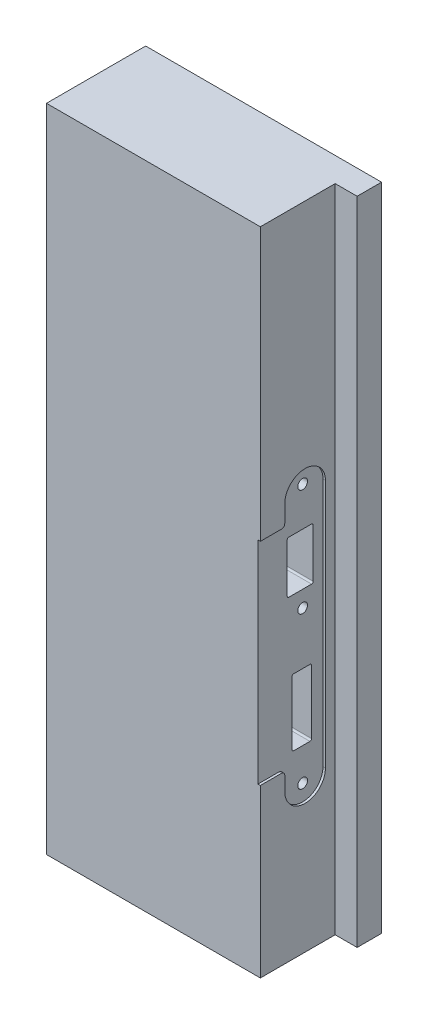
SolidWorks part; units mm, degrees
ref_plane "Plan de face" through (0, 0, 0) normal (0, 0, 1) x (1, 0, 0)
ref_plane "Plan de dessus" through (0, 0, 0) normal (0, 1, 0) x (1, 0, 0)
ref_plane "Plan de droite" through (0, 0, 0) normal (1, 0, 0) x (0, 0, -1)
sketch "Esquisse2" plane through (405.3935, 0, 0) normal (-1, 0, 0) x (0, 0, 1)
  line L0 (-30.5517, -238.2531) -> (-30.5517, -405.7531)
  line L1 (-30.5517, -535.7531) -> (-30.5517, -638.2531)
  line L2 (-30.5517, -407.7531) -> (-30.5517, -533.7531) construction
  line L4 (-76.5517, -238.2531) -> (-76.5517, -638.2531)
  line L5 (-76.5517, -638.2531) -> (-36.5517, -638.2531)
  line L6 (-70.5517, -393.2531) -> (-70.5517, -546.5031)
  line L7 (-45.5517, -546.5031) -> (-45.5517, -537.7531)
  line L8 (-43.5517, -535.7531) -> (-32.5517, -535.7531)
  line L9 (-30.5517, -533.7531) -> (-30.5517, -407.7531)
  line L10 (-32.5517, -405.7531) -> (-43.5517, -405.7531)
  line L11 (-45.5517, -403.7531) -> (-45.5517, -393.2531)
  line L12 (-70.5517, -393.2531) -> (-70.5517, -546.5031)
  line L13 (-45.5517, -546.5031) -> (-45.5517, -537.7531)
  line L14 (-43.5517, -535.7531) -> (-30.5517, -535.7531)
  line L16 (-30.5517, -405.7531) -> (-43.5517, -405.7531)
  line L17 (-45.5517, -403.7531) -> (-45.5517, -393.2531)
  line L18 (-36.5517, -638.2531) -> (-36.5517, -238.2531)
  line L19 (-36.5517, -238.2531) -> (-76.5517, -238.2531)
  line L20 (-76.5517, -238.2531) -> (-76.5517, -638.2531)
  line L21 (-76.5517, -638.2531) -> (-30.5517, -638.2531)
  line L23 (-30.5517, -238.2531) -> (-76.5517, -238.2531)
  arc A6 (-45.5517, -393.2531) -> (-70.5517, -393.2531) centre (-58.0517, -393.2531) ccw
  arc A7 (-70.5517, -546.5031) -> (-45.5517, -546.5031) centre (-58.0517, -546.5031) ccw
  arc A8 (-43.5517, -535.7531) -> (-45.5517, -537.7531) centre (-43.5517, -537.7531) ccw
  arc A9 (-32.5517, -535.7531) -> (-30.5517, -533.7531) centre (-32.5517, -533.7531) ccw
  arc A10 (-30.5517, -407.7531) -> (-32.5517, -405.7531) centre (-32.5517, -407.7531) ccw
  arc A11 (-45.5517, -403.7531) -> (-43.5517, -405.7531) centre (-43.5517, -403.7531) ccw
  arc A12 (-45.5517, -393.2531) -> (-70.5517, -393.2531) centre (-58.0517, -393.2531) ccw
  arc A13 (-70.5517, -546.5031) -> (-45.5517, -546.5031) centre (-58.0517, -546.5031) ccw
  arc A14 (-43.5517, -535.7531) -> (-45.5517, -537.7531) centre (-43.5517, -537.7531) ccw
  arc A17 (-45.5517, -403.7531) -> (-43.5517, -405.7531) centre (-43.5517, -403.7531) ccw
  dimension "D1" = 0
  dimension "D2" = 0
extrude "Extrusion1" add sketch "Esquisse2" against normal up to surface (1.5 mm away)
sketch "Esquisse3" plane through (405.3935, 0, 0) normal (-1, 0, 0) x (0, 0, 1)
  line L0 (-30.5517, -238.2531) -> (-76.5517, -238.2531) construction
  line L1 (-30.5517, -238.2531) -> (-76.5517, -238.2531)
  line L2 (-76.5517, -238.2531) -> (-76.5517, -638.2531) construction
  line L3 (-76.5517, -238.2531) -> (-76.5517, -638.2531)
  line L4 (-30.5517, -405.7531) -> (-30.5517, -238.2531) construction
  line L5 (-30.5517, -638.2531) -> (-30.5517, -238.2531)
  line L6 (-76.5517, -638.2531) -> (-30.5517, -638.2531) construction
  line L7 (-76.5517, -638.2531) -> (-30.5517, -638.2531)
extrude "Extrusion2" add sketch "Esquisse3" along normal blind 130
sketch "Esquisse4" plane through (275.3935, 0, 0) normal (-1, 0, 0) x (0, 0, 1)
  line L1 (-76.5517, -238.2531) -> (-91.5517, -238.2531)
  line L2 (-76.5517, -238.2531) -> (-76.5517, -638.2531)
  line L3 (-76.5517, -638.2531) -> (-91.5517, -638.2531)
  line L4 (-91.5517, -238.2531) -> (-91.5517, -638.2531)
  line L5 (-76.5517, -638.2531) -> (-30.5517, -638.2531) construction
  dimension "D1" = 15
extrude "Extrusion3" add sketch "Esquisse4" against normal blind 145
ref_plane "Plan1" through (520.3935, 0, 0) normal (1, 0, 0) x (0, 0, -1)
sketch "Esquisse6" plane through (520.3935, 0, 0) normal (1, 0, 0) x (0, 0, -1)
  line L4 (63.5517, -413.7531) -> (49.5517, -413.7531)
  line L5 (64.5517, -444.7531) -> (64.5517, -414.7531)
  line L18 (49.5517, -445.7531) -> (63.5517, -445.7531)
  line L19 (48.5517, -414.7531) -> (48.5517, -444.7531)
  line L20 (63.5517, -413.7531) -> (49.5517, -413.7531)
  line L21 (64.5517, -444.7531) -> (64.5517, -414.7531)
  line L22 (49.5517, -445.7531) -> (63.5517, -445.7531)
  line L23 (48.5517, -414.7531) -> (48.5517, -444.7531)
  line L24 (51.5517, -489.0031) -> (51.5517, -528.0031)
  line L25 (62.5517, -488.0031) -> (52.5517, -488.0031)
  line L26 (63.5517, -528.0031) -> (63.5517, -489.0031)
  line L27 (52.5517, -529.0031) -> (62.5517, -529.0031)
  line L28 (51.5517, -489.0031) -> (51.5517, -528.0031)
  line L29 (62.5517, -488.0031) -> (52.5517, -488.0031)
  line L30 (63.5517, -528.0031) -> (63.5517, -489.0031)
  line L31 (52.5517, -529.0031) -> (62.5517, -529.0031)
  circle A1 centre (58.0517, -389.7531) radius 3
  circle A2 centre (58.0517, -389.7531) radius 3
  circle A3 centre (58.0517, -455.7531) radius 3
  circle A4 centre (58.0517, -455.7531) radius 3
  circle A5 centre (58.0517, -549.0031) radius 3
  circle A6 centre (58.0517, -549.0031) radius 3
  arc A20 (64.5517, -414.7531) -> (63.5517, -413.7531) centre (63.5517, -414.7531) ccw
  arc A21 (63.5517, -445.7531) -> (64.5517, -444.7531) centre (63.5517, -444.7531) ccw
  arc A22 (48.5517, -444.7531) -> (49.5517, -445.7531) centre (49.5517, -444.7531) ccw
  arc A23 (49.5517, -413.7531) -> (48.5517, -414.7531) centre (49.5517, -414.7531) ccw
  arc A24 (64.5517, -414.7531) -> (63.5517, -413.7531) centre (63.5517, -414.7531) ccw
  arc A25 (63.5517, -445.7531) -> (64.5517, -444.7531) centre (63.5517, -444.7531) ccw
  arc A26 (48.5517, -444.7531) -> (49.5517, -445.7531) centre (49.5517, -444.7531) ccw
  arc A27 (49.5517, -413.7531) -> (48.5517, -414.7531) centre (49.5517, -414.7531) ccw
  arc A30 (51.5517, -528.0031) -> (52.5517, -529.0031) centre (52.5517, -528.0031) ccw
  arc A31 (52.5517, -488.0031) -> (51.5517, -489.0031) centre (52.5517, -489.0031) ccw
  arc A32 (63.5517, -489.0031) -> (62.5517, -488.0031) centre (62.5517, -489.0031) ccw
  arc A33 (62.5517, -529.0031) -> (63.5517, -528.0031) centre (62.5517, -528.0031) ccw
  arc A34 (51.5517, -528.0031) -> (52.5517, -529.0031) centre (52.5517, -528.0031) ccw
  arc A35 (52.5517, -488.0031) -> (51.5517, -489.0031) centre (52.5517, -489.0031) ccw
  arc A36 (63.5517, -489.0031) -> (62.5517, -488.0031) centre (62.5517, -489.0031) ccw
  arc A37 (62.5517, -529.0031) -> (63.5517, -528.0031) centre (62.5517, -528.0031) ccw
  dimension "D1" = 0
  dimension "D3" = 0
  dimension "D4" = 0
  dimension "D5" = 0
  dimension "D6" = 0
sketch "Esquisse7" plane through (405.3935, 0, 0) normal (1, 0, 0) x (0, 0, -1)
  line L4 (48.5517, -414.7531) -> (48.5517, -444.7531)
  line L5 (49.5517, -445.7531) -> (63.5517, -445.7531)
  line L6 (64.5517, -444.7531) -> (64.5517, -414.7531)
  line L7 (63.5517, -413.7531) -> (49.5517, -413.7531)
  line L8 (48.5517, -414.7531) -> (48.5517, -444.7531)
  line L9 (49.5517, -445.7531) -> (63.5517, -445.7531)
  line L10 (64.5517, -444.7531) -> (64.5517, -414.7531)
  line L11 (63.5517, -413.7531) -> (49.5517, -413.7531)
  line L12 (63.5517, -528.0031) -> (63.5517, -489.0031)
  line L13 (62.5517, -488.0031) -> (52.5517, -488.0031)
  line L14 (51.5517, -489.0031) -> (51.5517, -528.0031)
  line L15 (52.5517, -529.0031) -> (62.5517, -529.0031)
  line L16 (63.5517, -528.0031) -> (63.5517, -489.0031)
  line L17 (62.5517, -488.0031) -> (52.5517, -488.0031)
  line L18 (51.5517, -489.0031) -> (51.5517, -528.0031)
  line L19 (52.5517, -529.0031) -> (62.5517, -529.0031)
  circle A1 centre (58.0517, -389.7531) radius 3
  circle A2 centre (58.0517, -389.7531) radius 3
  circle A3 centre (58.0517, -455.7531) radius 3
  circle A4 centre (58.0517, -455.7531) radius 3
  circle A5 centre (58.0517, -549.0031) radius 3
  circle A6 centre (58.0517, -549.0031) radius 3
  arc A10 (48.5517, -444.7531) -> (49.5517, -445.7531) centre (49.5517, -444.7531) ccw
  arc A11 (63.5517, -445.7531) -> (64.5517, -444.7531) centre (63.5517, -444.7531) ccw
  arc A12 (64.5517, -414.7531) -> (63.5517, -413.7531) centre (63.5517, -414.7531) ccw
  arc A13 (49.5517, -413.7531) -> (48.5517, -414.7531) centre (49.5517, -414.7531) ccw
  arc A14 (48.5517, -444.7531) -> (49.5517, -445.7531) centre (49.5517, -444.7531) ccw
  arc A15 (63.5517, -445.7531) -> (64.5517, -444.7531) centre (63.5517, -444.7531) ccw
  arc A16 (64.5517, -414.7531) -> (63.5517, -413.7531) centre (63.5517, -414.7531) ccw
  arc A17 (49.5517, -413.7531) -> (48.5517, -414.7531) centre (49.5517, -414.7531) ccw
  arc A18 (63.5517, -489.0031) -> (62.5517, -488.0031) centre (62.5517, -489.0031) ccw
  arc A19 (52.5517, -488.0031) -> (51.5517, -489.0031) centre (52.5517, -489.0031) ccw
  arc A20 (51.5517, -528.0031) -> (52.5517, -529.0031) centre (52.5517, -528.0031) ccw
  arc A21 (62.5517, -529.0031) -> (63.5517, -528.0031) centre (62.5517, -528.0031) ccw
  arc A22 (63.5517, -489.0031) -> (62.5517, -488.0031) centre (62.5517, -489.0031) ccw
  arc A23 (52.5517, -488.0031) -> (51.5517, -489.0031) centre (52.5517, -489.0031) ccw
  arc A24 (51.5517, -528.0031) -> (52.5517, -529.0031) centre (52.5517, -528.0031) ccw
  arc A25 (62.5517, -529.0031) -> (63.5517, -528.0031) centre (62.5517, -528.0031) ccw
  dimension "D1" = 0
  dimension "D2" = 0
  dimension "D3" = 0
  dimension "D4" = 0
  dimension "D5" = 0
extrude "Enlèv. mat.-Extru.1" cut sketch "Esquisse7" against normal blind 20
